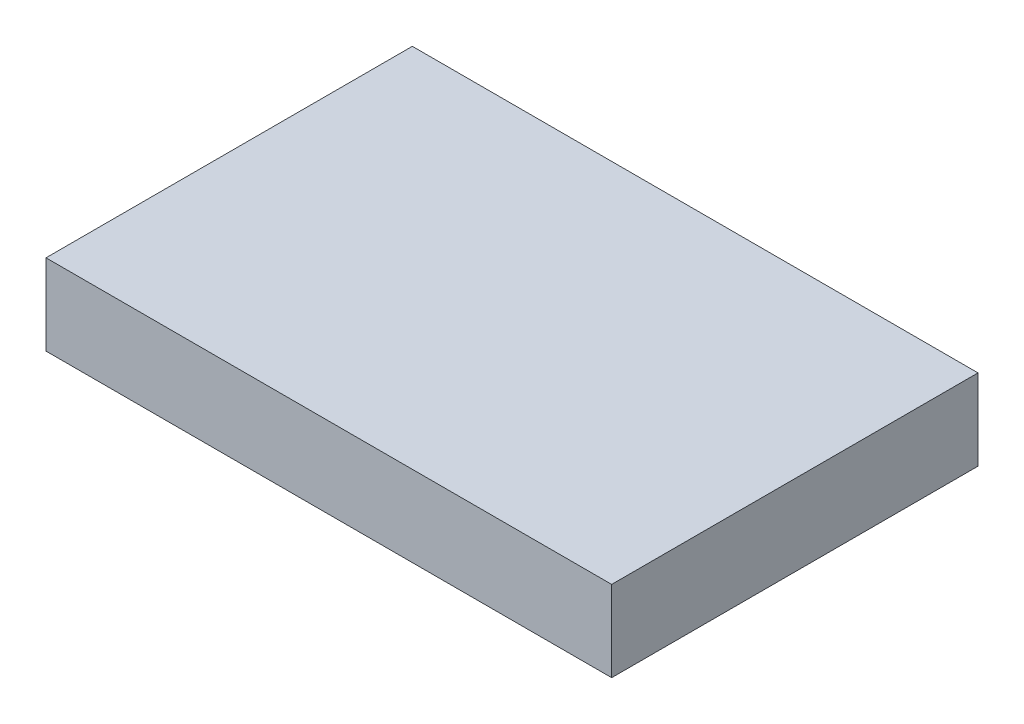
SolidWorks part; units mm, degrees
ref_plane "Front" through (0, 0, 0) normal (0, 0, 1) x (1, 0, 0)
ref_plane "Top" through (0, 0, 0) normal (0, 1, 0) x (1, 0, 0)
ref_plane "Right" through (0, 0, 0) normal (1, 0, 0) x (0, 0, -1)
sketch "Sketch1" plane through (0, 0, 0) normal (0, 1, 0) x (1, 0, 0)
  line L1 (0, 0) -> (21, 0)
  line L2 (0, 0) -> (0, -13.6)
  line L3 (0, -13.6) -> (21, -13.6)
  line L4 (21, 0) -> (21, -13.6)
  dimension "D1" = 13.6
  dimension "D2" = 21
extrude "Boss-Extrude1" add sketch "Sketch1" along normal blind 3
